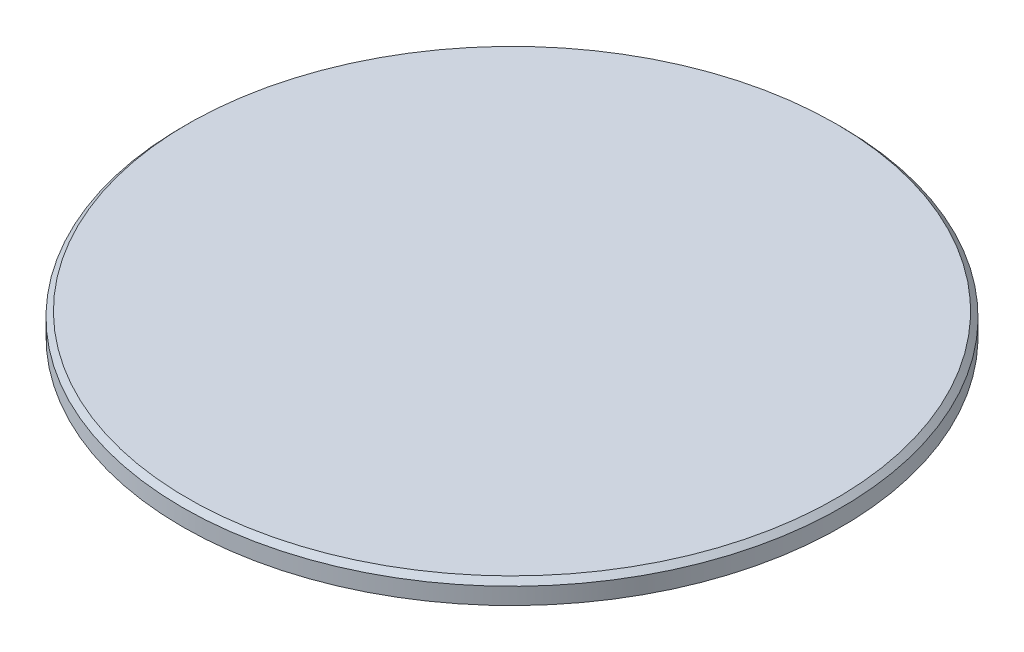
SolidWorks part; units mm, degrees
material "1060 Сплав"
ref_plane "Front Plane" through (0, 0, 0) normal (0, 0, 1) x (1, 0, 0)
ref_plane "Top Plane" through (0, 0, 0) normal (0, 1, 0) x (1, 0, 0)
ref_plane "Right Plane" through (0, 0, 0) normal (1, 0, 0) x (0, 0, -1)
sketch "Эскиз1" plane through (0, 0, 0) normal (0, 0, 1) x (1, 0, 0)
  line L0 (0, 0) -> (0, 17.9637) construction
  line L1 (0, 0) -> (-37.5, 0)
  line L2 (-37.5, 0) -> (-37.5, -2.5)
  line L3 (-37.5, -2.5) -> (-24.65, -2.5)
  line L4 (-24.65, -2.5) -> (-24.65, -5.5)
  line L5 (-24.65, -5.5) -> (-20, -5.5)
  line L6 (-20, -5.5) -> (-20, -2.5)
  line L7 (-20, -2.5) -> (0, -2.5)
  line L8 (0, -2.5) -> (0, 0)
  dimension "D1" = 49.3
  dimension "D2" = 40
  dimension "D3" = 2.5
  dimension "D5" = 75
  dimension "D6" = 3
revolve "Повернуть1" add sketch "Эскиз1" angle 360 about L0
sketch "Эскиз3" plane through (0, -2.5, 0) normal (0, -1, 0) x (1, 0, 0)
  line L1 (-14.0816, 11.96) -> (-17.3985, -6.215)
  line L2 (-17.3985, -6.215) -> (-3.3169, -18.175)
  line L3 (-3.3169, -18.175) -> (14.0816, -11.96)
  line L4 (14.0816, -11.96) -> (17.3985, 6.215)
  line L5 (17.3985, 6.215) -> (3.3169, 18.175)
  line L6 (3.3169, 18.175) -> (-14.0816, 11.96)
  circle A0 centre (0, 0) radius 16 construction
  dimension "D1" = 32
sketch "Эскиз4" plane through (0, -2.5, 0) normal (0, -1, 0) x (1, 0, 0)
  circle A0 centre (0, 0) radius 31 construction
  circle A1 centre (-31, 0) radius 4
  dimension "D1" = 62
  dimension "D2" = 8
extrude "Вырез-Вытянуть1" cut sketch "Эскиз4" against normal blind 2
pattern_circular "Круговой массив1" count 6 over 360 about axis through (0, 0, 0) along (0, 1, 0) of "Вырез-Вытянуть1"
chamfer "Фаска1" distance 0.6 angle 45 2 edges at (0, 0, -37.5) (0, -5.5, -24.65)
sketch "Эскиз5" plane through (0, -5.5, 0) normal (0, -1, 0) x (1, 0, 0)
  line L0 (0, 0) -> (23.25, -13.4234)
  line L1 (15.5, -26.8468) -> (31, 0) construction
  point P7 (23.25, -13.4234)
extrude "Вырез-Вытянуть-Тонкостенный1" [suppressed] cut sketch "Эскиз5" against normal up to surface and the other way through all thin
pattern_circular "Круговой массив2" [suppressed] count 6 over 360
